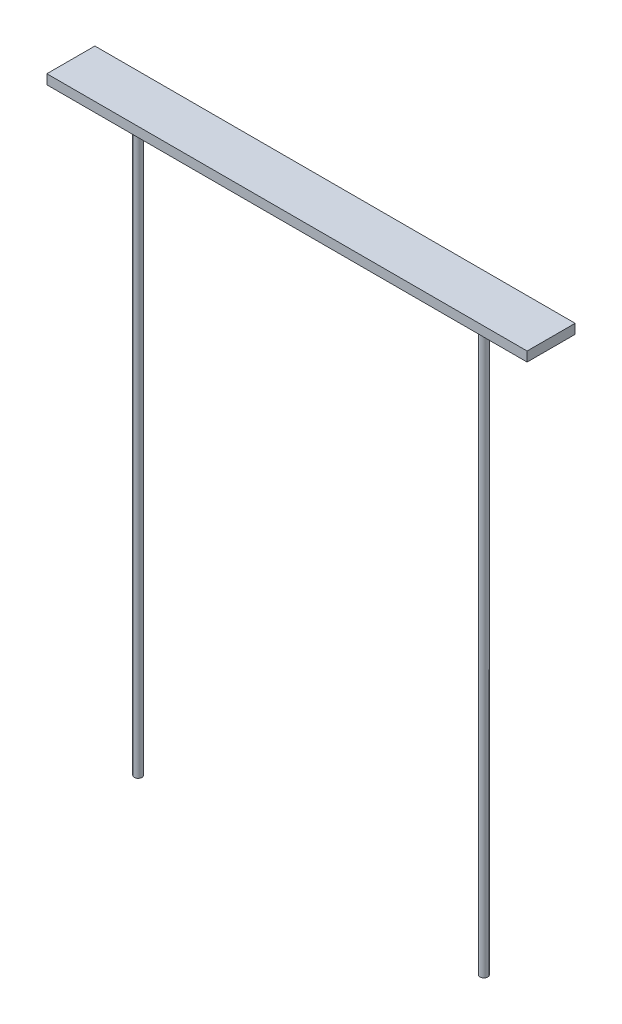
SolidWorks part; units mm, degrees
material "Stainless Steel (ferritic)"
ref_plane "Front Plane" through (0, 0, 0) normal (0, 0, 1) x (1, 0, 0)
ref_plane "Top Plane" through (0, 0, 0) normal (0, 1, 0) x (1, 0, 0)
ref_plane "Right Plane" through (0, 0, 0) normal (1, 0, 0) x (0, 0, -1)
sketch "Sketch1" plane through (0, 0, 0) normal (0, 1, 0) x (1, 0, 0)
  line L1 (-250, 25) -> (250, 25)
  line L2 (-250, 25) -> (-250, -25)
  line L3 (-250, -25) -> (250, -25)
  line L4 (250, 25) -> (250, -25)
  line L5 (-250, 25) -> (250, -25) construction
  line L6 (-250, -25) -> (250, 25) construction
  point P0 (0, 0)
extrude "Boss-Extrude1" add sketch "Sketch1" along normal blind 10
sketch "Sketch2" plane through (0, 0, 0) normal (0, -1, 0) x (1, 0, 0)
  circle A0 centre (180, 0) radius 4
extrude "Boss-Extrude2" add sketch "Sketch2" along normal blind 600
sketch "Sketch4" plane through (0, 0, 0) normal (0, -1, 0) x (1, 0, 0)
  circle A0 centre (125, 0) radius 4
sketch "Sketch6" plane through (0, 0, 0) normal (0, -1, 0) x (1, 0, 0)
  circle A0 centre (-180, 0) radius 4
extrude "Boss-Extrude3" add sketch "Sketch6" along normal blind 600
sketch "Sketch7" plane through (0, 0, 0) normal (0, -1, 0) x (-1, 0, 0)
  circle A0 centre (125, 0) radius 4
sketch "Sketch9" plane through (0, 10, 0) normal (0, 1, 0) x (1, 0, 0)
  circle A0 centre (0, 0) radius 4
  dimension "D1" = 8
